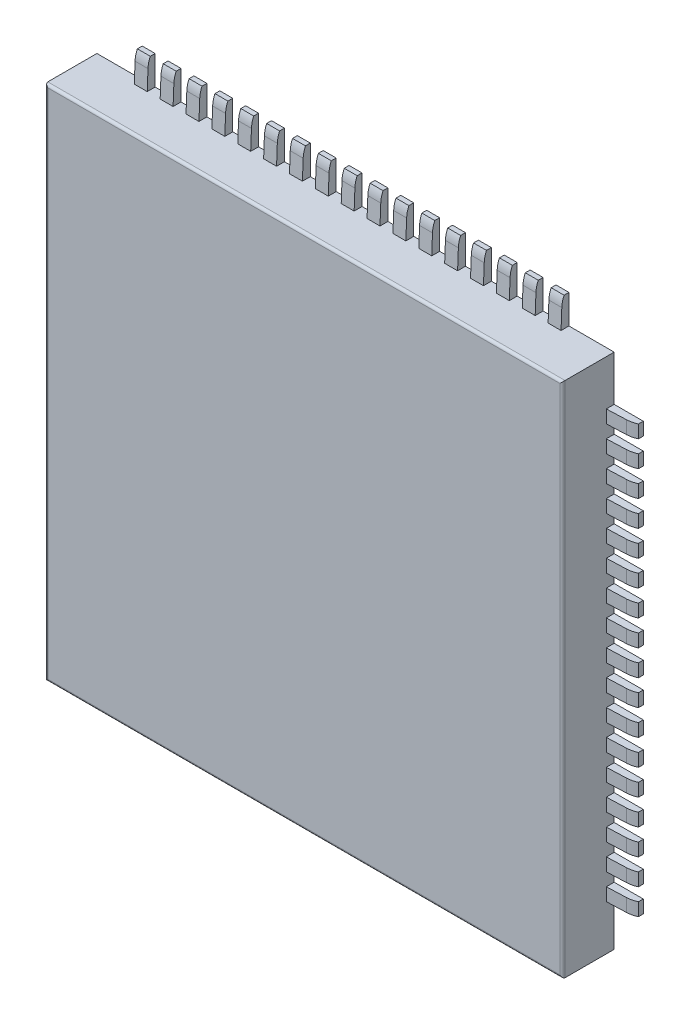
SolidWorks part; units mm, degrees
ref_plane "Płaszczyzna przednia" through (0, 0, 0) normal (0, 0, 1) x (1, 0, 0)
ref_plane "Płaszczyzna górna" through (0, 0, 0) normal (0, 1, 0) x (1, 0, 0)
ref_plane "Płaszczyzna prawa" through (0, 0, 0) normal (1, 0, 0) x (0, 0, -1)
sketch "Sketch1" plane through (0, 0, 0) normal (0, 0, 1) x (1, 0, 0)
  line L1 (4, -4) -> (-4, -4)
  line L2 (4, -4) -> (4, 4)
  line L3 (4, 4) -> (-4, 4)
  line L4 (-4, -4) -> (-4, 4)
  line L5 (4, -4) -> (-4, 4) construction
  line L6 (4, 4) -> (-4, -4) construction
  point P0 (0, 0)
  dimension "D1" = 8
extrude "Boss-Extrude1" add sketch "Sketch1" along normal blind 0.8
fillet "Fillet1" radius 0.04 4 edges at (0, 4, 0.8) (4, 0, 0.8) (0, -4, 0.8) (-4, 0, 0.8)
sketch "Sketch2" plane through (0, 0, 0.8) normal (0, 0, 1) x (1, 0, 0)
  line L0 (1.5285, -1.7789) -> (1.5285, 2.8946) construction
  text T0 "rr"
sketch "Sketch3" plane through (0, 0, 0) normal (0, 0, -1) x (-1, 0, 0)
  line L0 (3.3, -4) -> (3.3, -4.45)
  line L1 (-4, -4) -> (4, -4) construction
  line L2 (3.3, -4.45) -> (3.1, -4.45)
  line L3 (3.1, -4.45) -> (3.1, -4)
  line L4 (3.1, -4) -> (3.3, -4)
  line L5 (4, -4) -> (4, 4) construction
  dimension "D1" = 0.7
  dimension "D2" = 0.2
  dimension "D3" = 0.45
extrude "Boss-Extrude2" add sketch "Sketch3" against normal blind 0.15 separate body
sketch "Sketch4" plane through (-3.3, 0, 0) normal (-1, 0, 0) x (0, 0, 1)
  line L7 (0.1219, -4) -> (0.1102, -4.3019)
  line L8 (0.76, -4) -> (0, -4) construction
  line L9 (0.15, -4.45) -> (0, -4.45) construction
  line L10 (0.1219, -4) -> (0.2931, -4)
  line L11 (0.2931, -4) -> (0.2724, -4.5922)
  line L12 (0.2724, -4.5922) -> (0.075, -4.45)
  arc A1 (0.1102, -4.3019) -> (0.075, -4.45) centre (-0.284, -4.2866) cw
extrude "Cut-Extrude2" cut sketch "Sketch4" against normal through all
pattern_linear "LPattern1" count 17 spacing 0.4 along (1, 0, 0) of bodies 151 104
sketch "Sketch5" plane through (0, 0, 0) normal (0, 0, -1) x (-1, 0, 0)
  circle A0 centre (0, 0) radius 2.5
  dimension "D1" = 5
extrude "Boss-Extrude3" add sketch "Sketch5" along normal blind 0.1 separate body
pattern_circular "CirPattern1" count 4 over 360 about axis through (0, 0, 0) along (0, 0, 1) of bodies 150 149 148 147 146 145 144 143 151 105 106 107 108 109 110 111 112 104
